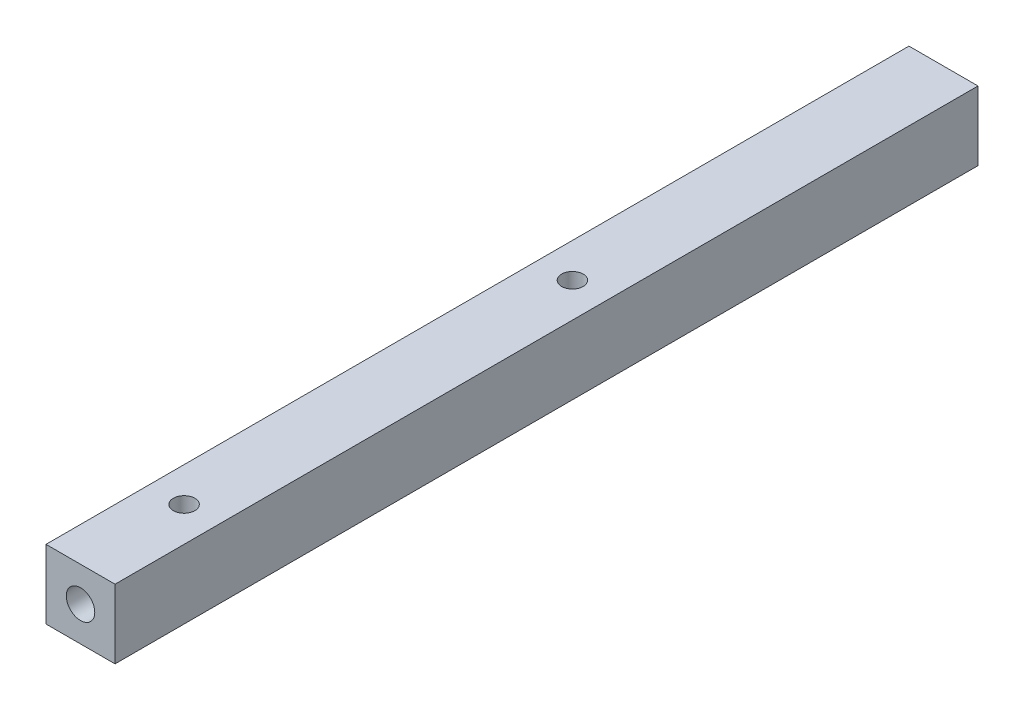
SolidWorks part; units mm, degrees
ref_plane "Front Plane" through (0, 0, 0) normal (0, 0, 1) x (1, 0, 0)
ref_plane "Top Plane" through (0, 0, 0) normal (0, 1, 0) x (1, 0, 0)
ref_plane "Right Plane" through (0, 0, 0) normal (1, 0, 0) x (0, 0, -1)
sketch "Sketch1" plane through (0, 0, 0) normal (0, 0, 1) x (1, 0, 0)
  line L1 (0, 0) -> (8, 0)
  line L2 (0, 0) -> (0, 8)
  line L3 (0, 8) -> (8, 8)
  line L4 (8, 0) -> (8, 8)
extrude "Extrude1" add sketch "Sketch1" along normal blind 100
sketch "Sketch2" plane through (0, 8, 0) normal (0, 1, 0) x (1, 0, 0)
  line L0 (4, -100) -> (4, -88) construction
  line L1 (8, -100) -> (0, -100) construction
  line L2 (4, -88) -> (4, -43) construction
  line L3 (4, -43) -> (4, 0) construction
  line L4 (8, 0) -> (0, 0) construction
hole_wizard "M3 Tapped Hole1" positions "3DSketch1" profile "Sketch3" tap size "M3" standard "DIN" end condition through all
sketch3d "3DSketch1"
  point P0 (4, 8, 88)
  point P3 (4, 8, 43)
sketch "Sketch3" plane through (4, 8, 88) normal (1, 0, 0) x (0, 0, 1)
  line L0 (0, 0) -> (0, 8)
  line L1 (0, 8) -> (1.25, 8)
  line L2 (1.25, 8) -> (1.25, 0)
  line L5 (1.25, 0) -> (0, 0)
  line L11 (0, -6.35) -> (0, 107.95) construction
  dimension "Thru Tap Drill Dia." = 2.5
  dimension "Thru Tap Drill Depth" = 8
cosmetic thread "Hole Thread1"
cosmetic thread "Hole Thread2"
sketch "Sketch4" plane through (0, 0, 100) normal (0, 0, 1) x (1, 0, 0)
  line L0 (0, 4) -> (8, 4) construction
  line L1 (0, 8) -> (0, 0) construction
  line L2 (8, 0) -> (8, 8) construction
  point P6 (4, 4)
sketch "Sketch5" plane through (0, 0, 0) normal (0, 0, -1) x (-1, 0, 0)
  line L0 (-8, 4) -> (0, 4) construction
  line L1 (-8, 0) -> (-8, 8) construction
  line L2 (0, 8) -> (0, 0) construction
  point P6 (-4, 4)
hole_wizard "M4 Tapped Hole1" positions "3DSketch2" profile "Sketch6" tap size "M4" standard "DIN"
sketch3d "3DSketch2"
  point P0 (4, 4, 100)
  point P3 (4, 4, 0)
sketch "Sketch6" plane through (4, 4, 100) normal (1, 0, 0) x (0, -1, 0)
  line L0 (0, 0) -> (0, 10.9914)
  line L1 (0, 10.9914) -> (1.65, 10)
  line L2 (1.65, 10) -> (1.65, 0)
  line L5 (1.65, 0) -> (0, 0)
  line L10 (0, 10.9914) -> (-1.65, 10) construction
  line L11 (0, -6.35) -> (0, 107.95) construction
  dimension "Tap Drill Dia." = 3.3
  dimension "Tap Drill Depth" = 10
  dimension "Drill Angle" = 118
cosmetic thread "Hole Thread3"
cosmetic thread "Hole Thread4"
